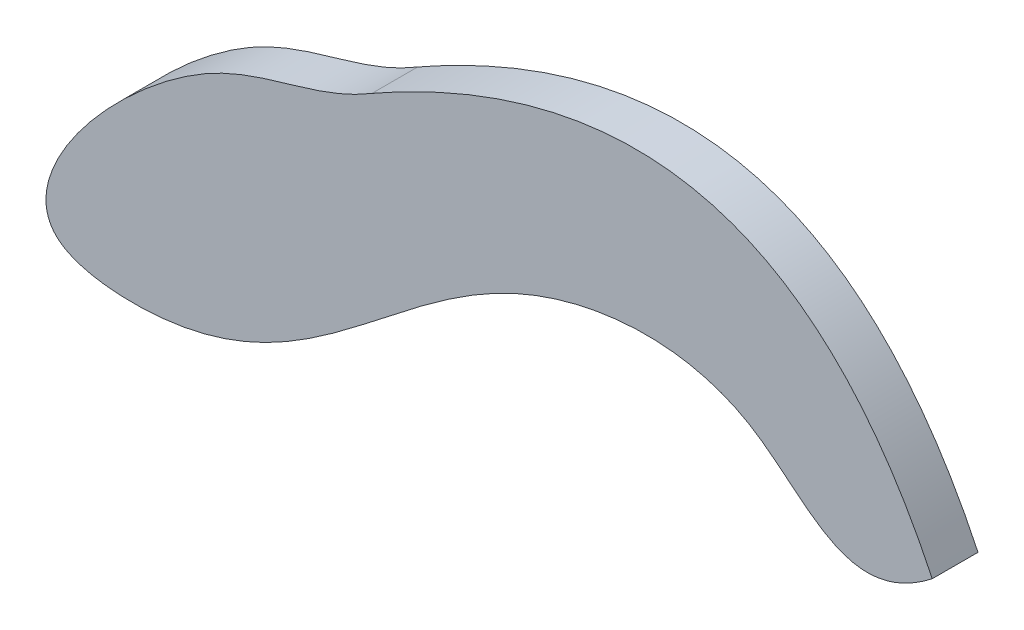
SolidWorks part; units mm, degrees
ref_plane "Front Plane" through (0, 0, 0) normal (0, 0, 1) x (1, 0, 0)
ref_plane "Top Plane" through (0, 0, 0) normal (0, 1, 0) x (1, 0, 0)
ref_plane "Right Plane" through (0, 0, 0) normal (1, 0, 0) x (0, 0, -1)
sketch "Sketch1" plane through (0, 0, 0) normal (0, 0, 1) x (1, 0, 0)
  spline S1 degree 2 poles (-73.8513, 4.7922) (-14.3553, 38.5734) (11.9034, -16.6465) knots 0 0 0 1 1 1
  spline S2 degree 3 poles (11.9034, -16.6465) (-1.1431, -26.8274) (-13.7058, -3.2043) (-64.7012, -7.7098) (-85.4931, -44.0141) (-135.9428, -39.4316) (-101.0088, 0.4148) (-82.5282, -0.435) (-73.8513, 4.7922) knots 0 0 0 0 0.144374 0.307193 0.610895 0.682012 0.87353 1 1 1 1
extrude "Boss-Extrude1" add sketch "Sketch1" along normal blind 7
